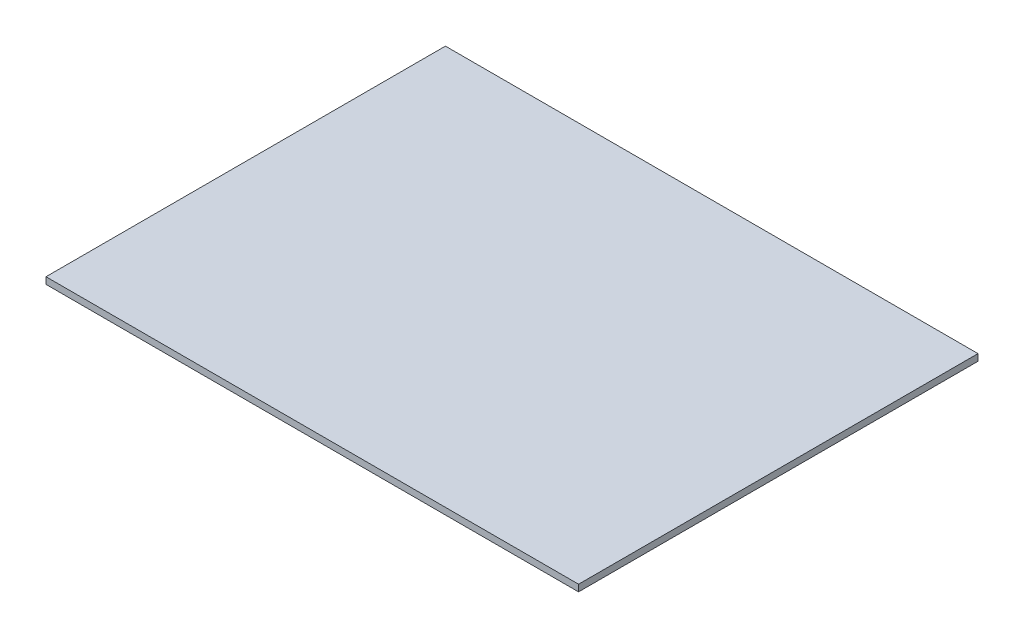
SolidWorks part; units mm, degrees
material "Chêne"
ref_plane "Plan de face" through (0, 0, 0) normal (0, 0, 1) x (1, 0, 0)
ref_plane "Plan de dessus" through (0, 0, 0) normal (0, 1, 0) x (1, 0, 0)
ref_plane "Plan de droite" through (0, 0, 0) normal (1, 0, 0) x (0, 0, -1)
sketch "Esquisse1" plane through (0, 0, 0) normal (0, 1, 0) x (1, 0, 0)
  line L1 (0, 0) -> (240, 0)
  line L2 (0, 0) -> (0, 180)
  line L3 (0, 180) -> (240, 180)
  line L4 (240, 0) -> (240, 180)
  dimension "D1" = 180
  dimension "D2" = 240
extrude "Boss.-Extru.1" add sketch "Esquisse1" along normal blind 3
